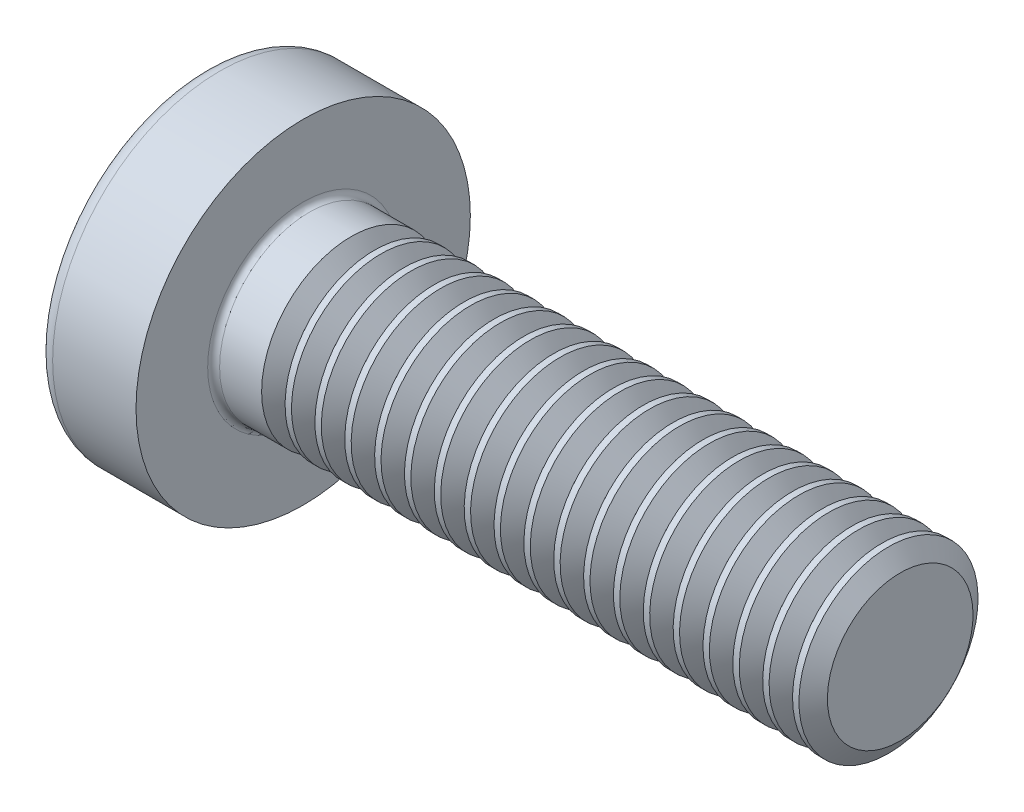
SolidWorks part; units mm, degrees
ref_plane "Plane1" through (0, 0, 0) normal (0, 0, 1) x (1, 0, 0)
ref_plane "Plane2" through (0, 0, 0) normal (0, 1, 0) x (1, 0, 0)
ref_plane "Plane3" through (0, 0, 0) normal (1, 0, 0) x (0, 0, -1)
sketch "BodySke" plane through (0, 0, 0) normal (0, 0, 1) x (1, 0, 0)
  line L0 (2.4, 1.5) -> (2.4, 2.8)
  line L1 (2.65, 6.35) -> (2.65, -3.175) construction
  line L2 (-25.4, 0) -> (127, 0) construction
  line L3 (12.4, 0) -> (0, 0)
  line L4 (2.4, 1.5) -> (12.4, 1.5)
  line L5 (12.4, 1.5) -> (12.4, 0)
  line L6 (1.0035, 2.8) -> (2.4, 2.8)
  line L8 (2.4, 6.35) -> (2.4, -3.175) construction
  arc A0 (0.7754, 2.6744) -> (0, 0) centre (5, 0) ccw
  arc A2 (0.7754, 2.6744) -> (1.0035, 2.8) centre (1.0035, 2.53) cw
  dimension "Head_fillet_rad" = 0.27
  dimension "Head_crown_rad" = 5
  dimension "Head_ht" = 2.4
  dimension "Diameter" = 3
  dimension "Length" = 10
  dimension "Head_dia" = 5.6
  dimension "Advance" = 0.5
  dimension "Thread_nom" = 10
revolve "Base-Revolve" add sketch "BodySke" angle 360 about L2
cosmetic thread "ThreadCosmetic" [suppressed] parameters "Thread_length"=9, "Thread_minor"=2.439
fillet "Fillet1" radius 0.1 1 edges at (2.4, 0, 1.5)
sketch "Sketch3" plane through (0, 0, 0) normal (1, 0, 0) x (0, 0, -1)
  line L0 (0.37, -1.4) -> (-0.37, -1.4)
  line L1 (0.37, -1.4) -> (0.37, 1.4)
  line L2 (-0.37, 1.4) -> (0.37, 1.4)
  line L3 (-0.37, 1.4) -> (-0.37, -1.4)
  dimension "D1" = 1.4
  dimension "Cross_dia" = 2.8
  dimension "D2" = 0.37
  dimension "Cross_width" = 0.74
ref_plane "Plane4" through (1.75, 0, 0) normal (1, 0, 0) x (0, 0, -1)
sketch "Sketch4" plane through (1.75, 0, 0) normal (1, 0, 0) x (0, 0, -1)
  line L0 (0.37, -0.5275) -> (-0.37, -0.5275)
  line L1 (0.37, -0.5275) -> (0.37, 0.5275)
  line L2 (-0.37, 0.5275) -> (0.37, 0.5275)
  line L3 (-0.37, 0.5275) -> (-0.37, -0.5275)
  dimension "D1" = 0.74
  dimension "D2" = 1.055
  dimension "D3" = 0.37
  dimension "D4" = 0.5275
loft "Recess" cut profiles "Sketch3", "Sketch4"
pattern_circular "RecPat" count 2 every 90 about axis through (0, 0, 0) along (1, 0, 0) of "Recess"
sketch "RecCorSke" plane through (0, 0, 0) normal (0, 0, 1) x (1, 0, 0)
  line L0 (-3.175, 0) -> (15.875, 0) construction
  line L1 (-25.4, 0) -> (127, 0) construction
  line L2 (0, 0) -> (0, 0.6784)
  line L3 (0, 0.6784) -> (1.75, 0.556)
  line L4 (1.75, 0.556) -> (1.9307, 0)
  line L5 (1.9307, 0) -> (0, 0)
  dimension "Diameter" = 1.112
  dimension "Depth" = 1.75
  dimension "Draft_angle" = 4
  dimension "Bottom_angle" = 18
revolve "RecessCore" cut sketch "RecCorSke" angle 360 about L0
sketch "ThdSchSke" plane through (0, 0, 0) normal (0, 0, 1) x (1, 0, 0)
  line L0 (3.4, -1.2195) -> (3.2036, -1.5)
  line L1 (3.4, -1.2195) -> (3.5964, -1.5)
  line L2 (3.5964, -1.5) -> (3.5964, -1.875)
  line L3 (-3.175, 0) -> (5.1513, 0) construction
  line L5 (3.5964, -1.875) -> (3.2036, -1.875)
  line L6 (3.2036, -1.875) -> (3.2036, -1.5)
  dimension "Thread_minor" = 2.439
  dimension "Diameter" = 3
  dimension "Start" = 3.4
  dimension "SideAngle" = 55
  dimension "VeeAngle" = 70
  dimension "Overcut" = 3.75
revolve "ThreadSchematic" cut sketch "ThdSchSke" angle 360 about L3
pattern_linear "ThdSchPat" count 19 spacing 0.5 along (1, 0, 0) of "ThreadSchematic"
equation "\"D1@Sketch3\" = \"Cross_dia@Sketch3\" / 2"
equation "\"D2@Sketch3\" = \"Cross_width@Sketch3\" / 2"
equation "\"Depth@RecCorSke\" = \"Cross_depth@Plane4\""
equation "\"D1@Sketch4\" = \"Cross_width@Sketch3\""
equation "\"D2@Sketch4\" = \"Cross_dia@Sketch3\" - 2.0 * \"Cross_depth@Plane4\" * tan(26.5  * 0.017453292)"
equation "\"D3@Sketch4\" = \"D1@Sketch4\" / 2"
equation "\"D4@Sketch4\" = \"D2@Sketch4\" / 2"
equation "\"Thread_length@ThreadCosmetic\" = ((sgn( (\"Length@BodySke\" - \"Advance@BodySke\" * 2.0 ) - \"Thread_nom@BodySke\" )-1)*( (\"Length@BodySke\" - \"Advance@BodySke\" * 2.0 ) - \"Thread_nom@BodySke\" ))/-2+ \"Thread_nom@BodySke\""
equation "\"Thread_minor@ThdSchSke\" = \"Thread_minor@ThreadCosmetic\""
equation "\"Diameter@ThdSchSke\" = \"Diameter@BodySke\""
equation "\"Overcut@ThdSchSke\" = \"Diameter@BodySke\" * 1.25"
equation "\"Start@ThdSchSke\" = \"Head_ht@BodySke\" + \"Length@BodySke\" - \"Thread_length@ThreadCosmetic\"  '---Non-countersunk---"
equation "\"Num_threads@ThdSchPat\" = int( \"Thread_length@ThreadCosmetic\" / \"Advance@BodySke\" + 0.999 )  + 1"
equation "\"Advance@ThdSchPat\" = \"Thread_length@ThreadCosmetic\" /  (\"Num_threads@ThdSchPat\" - 1) 'relax it"
